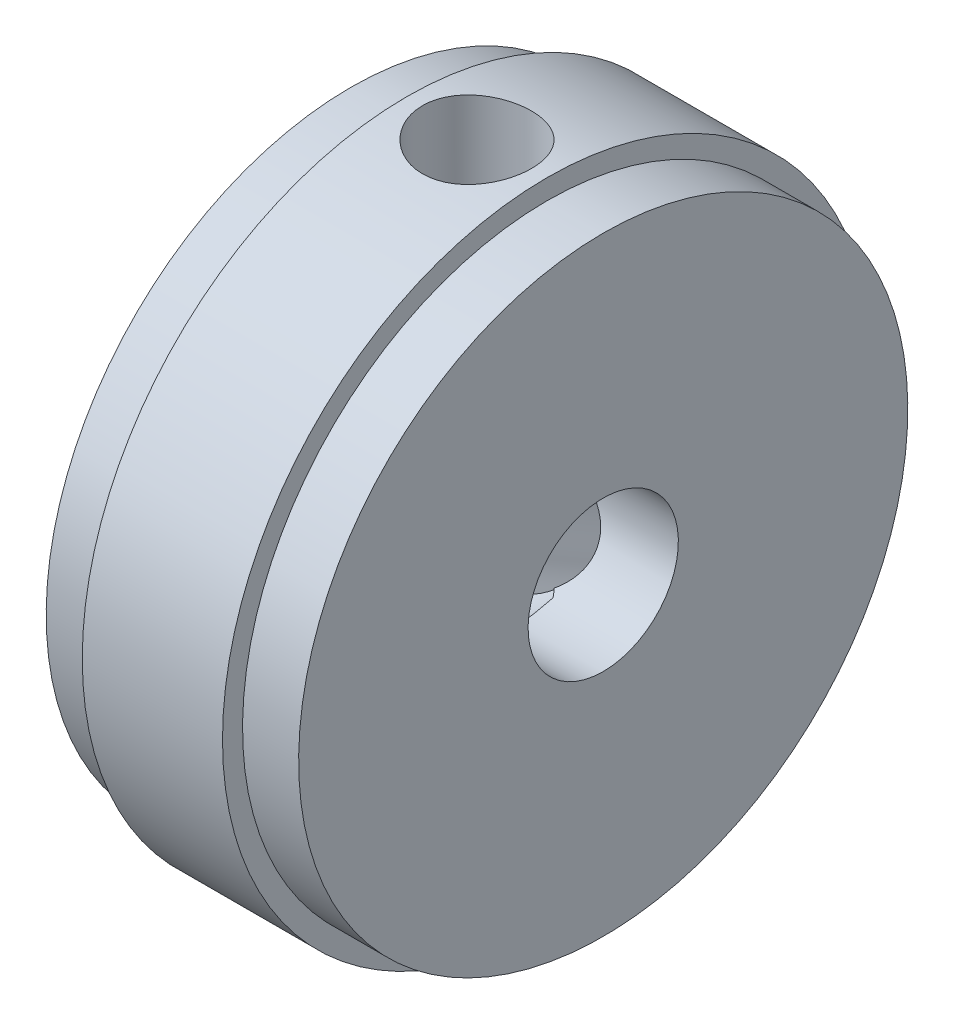
SolidWorks part; units mm, degrees
ref_plane "Front Plane" through (0, 0, 0) normal (0, 0, 1) x (1, 0, 0)
ref_plane "Top Plane" through (0, 0, 0) normal (0, 1, 0) x (1, 0, 0)
ref_plane "Right Plane" through (0, 0, 0) normal (1, 0, 0) x (0, 0, -1)
sketch "Sketch1" plane through (0, 0, 0) normal (0, 0, 1) x (1, 0, 0)
  line L0 (4, 0) -> (-4, 0)
  line L1 (-4, 0) -> (-4, 9.652)
  line L2 (-4, 9.652) -> (-2.222, 9.652)
  line L3 (-2.222, 9.652) -> (-2.222, 10.287)
  line L4 (-2.222, 10.287) -> (2.222, 10.287)
  line L5 (0, 6.9798) -> (0, -1.4779) construction
  line L6 (2.222, 9.652) -> (2.222, 10.287)
  line L7 (4, 9.652) -> (2.222, 9.652)
  line L8 (4, 0) -> (4, 9.652)
  line L9 (8.4308, 0) -> (-8.6385, 0) construction
  point P10 (0, 10.287)
  point P13 (0, 0)
  dimension "D1" = 4
  dimension "D2" = 1.778
  dimension "D3" = 9.652
  dimension "D4" = 0.635
revolve "Revolve1" add sketch "Sketch1" angle 360 about L9
sketch "Sketch2" plane through (-4, 0, 0) normal (-1, 0, 0) x (0, 0, 1)
  circle A0 centre (0, 0) radius 2.3813
  dimension "D1" = 4.7625
extrude "Cut-Extrude1" cut sketch "Sketch2" against normal through all
sketch "Sketch3" plane through (0, 0, 0) normal (1, 0, 0) x (0, 0, -1)
  line L0 (0, 0) -> (0, 10.287) construction
  circle A0 centre (0, 0) radius 10.287 construction
ref_plane "Plane1" through (0, 10.287, 0) normal (0, 1, 0) x (-1, 0, 0)
hole_wizard "#8-32 Tapped Hole1" positions "Sketch5" profile "Sketch4" tap size "#8-32" standard "Ansi Inch"
sketch "Sketch5" plane through (0, 10.287, 0) normal (0, 1, 0) x (-1, 0, 0)
  point P0 (0, 0)
sketch "Sketch4" plane through (0, 10.287, 0) normal (1, 0, 0) x (0, 0, 1)
  line L0 (0, 0) -> (0, 13.4838)
  line L1 (0, 13.4838) -> (1.7272, 12.446)
  line L2 (1.7272, 12.446) -> (1.7272, 0)
  line L5 (1.7272, 0) -> (0, 0)
  line L10 (0, 13.4838) -> (-1.7272, 12.446) construction
  line L11 (0, -6.35) -> (0, 107.95) construction
  dimension "Tap Drill Dia." = 3.4544
  dimension "Tap Drill Depth" = 12.446
  dimension "Drill Angle" = 118
sketch "Sketch9" plane through (4, 0, 0) normal (1, 0, 0) x (0, 0, -1)
  point P0 (0, 0)
pattern_circular "CirPattern1" count 2 over 120 about axis through (4, 0, 0) along (-1, 0, 0) of "#8-32 Tapped Hole1"
